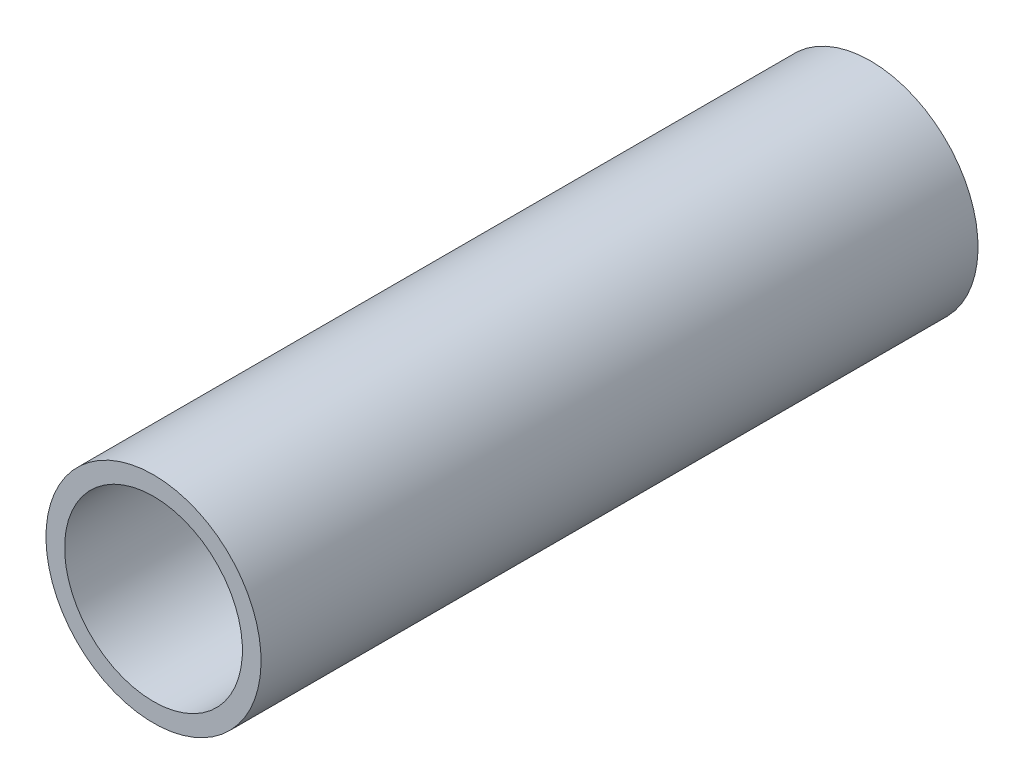
SolidWorks part; units mm, degrees
material "Plain Carbon Steel"
ref_plane "Front Plane" through (0, 0, 0) normal (0, 0, 1) x (1, 0, 0)
ref_plane "Top Plane" through (0, 0, 0) normal (0, 1, 0) x (1, 0, 0)
ref_plane "Right Plane" through (0, 0, 0) normal (1, 0, 0) x (0, 0, -1)
sketch "Sketch1" plane through (0, 0, 0) normal (1, 0, 0) x (0, 0, -1)
  line L0 (0, 0) -> (-32.9898, 0) construction
  line L1 (-31.75, 7.874) -> (31.75, 7.874)
  line L2 (31.75, 7.874) -> (31.75, 9.525)
  line L3 (31.75, 9.525) -> (-31.75, 9.525)
  line L4 (-31.75, 9.525) -> (-31.75, 7.874)
  point P7 (0, 7.874)
  dimension "D1" = 1.651
  dimension "D2" = 9.525
  dimension "D3" = 63.5
revolve "Revolve1" add sketch "Sketch1" angle 360 about L0
